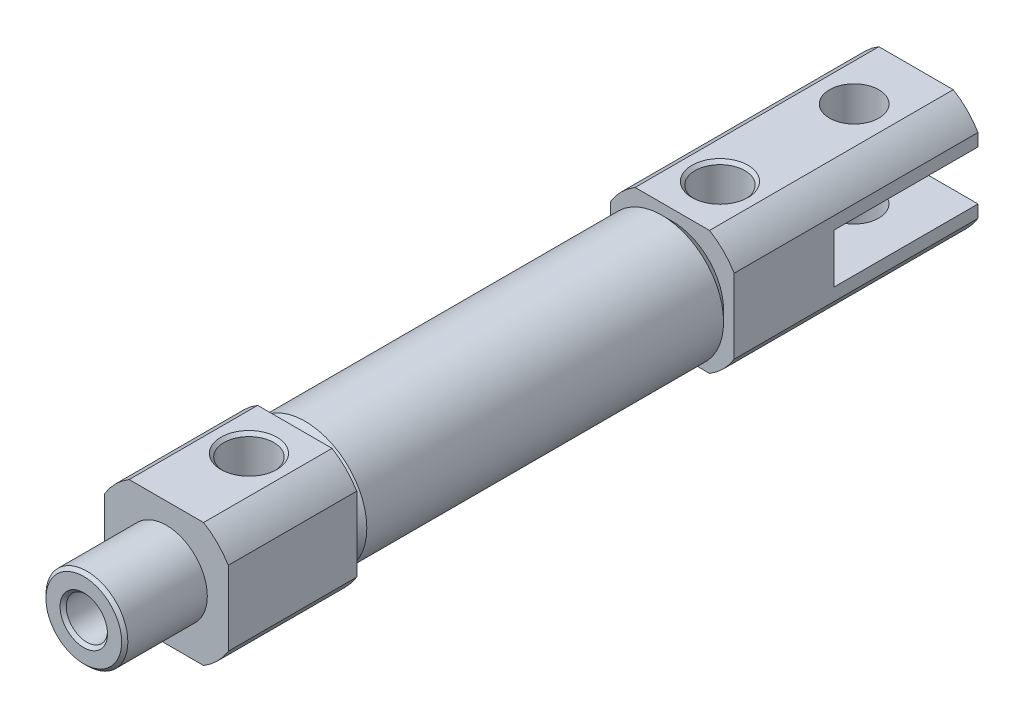
SolidWorks part; units mm, degrees
ref_plane "Front" through (0, 0, 0) normal (0, 0, 1) x (1, 0, 0)
ref_plane "Top" through (0, 0, 0) normal (0, 1, 0) x (1, 0, 0)
ref_plane "Right" through (0, 0, 0) normal (1, 0, 0) x (0, 0, -1)
sketch "Sketch1" plane through (0, 0, 0) normal (0, 0, 1) x (1, 0, 0)
  circle A0 centre (0, 0) radius 5.97
  dimension "D1" = 11.94
extrude "Base-Extrude" add sketch "Sketch1" along normal up to surface (18.285 mm away) and the other way up to surface (18.285 mm away)
chamfer "TubeChamfer" distance 1 angle 45 2 edges at (5.97, 0, 18.285) (5.97, 0, -18.285)
sketch "Sketch2" plane through (0, 0, 18.285) normal (0, 0, 1) x (1, 0, 0)
  line L1 (-3.6056, 6) -> (3.6056, 6)
  line L2 (-6, 3.6056) -> (-6, -3.6056)
  line L3 (-3.6056, -6) -> (3.6056, -6)
  line L4 (6, 3.6056) -> (6, -3.6056)
  arc A0 (6, 3.6056) -> (3.6056, 6) centre (0, 0) ccw
  arc A1 (3.6056, -6) -> (6, -3.6056) centre (0, 0) ccw
  arc A2 (-6, -3.6056) -> (-3.6056, -6) centre (0, 0) ccw
  arc A3 (-3.6056, 6) -> (-6, 3.6056) centre (0, 0) ccw
  point P4 (0, 5.6647)
  point P5 (-5.6647, 0)
  dimension "C" = 14
  dimension "B" = 12
extrude "RodCover" add sketch "Sketch2" along normal blind 12.45
sketch "Sketch3" plane through (0, 0, -18.285) normal (0, 0, -1) x (-1, 0, 0)
  line L1 (-3.6056, 6) -> (3.6056, 6)
  line L2 (-6, 3.6056) -> (-6, -3.6056)
  line L3 (-3.6056, -6) -> (3.6056, -6)
  line L4 (6, 3.6056) -> (6, -3.6056)
  arc A0 (-3.6056, 6) -> (-6, 3.6056) centre (0, 0) ccw
  arc A1 (-6, -3.6056) -> (-3.6056, -6) centre (0, 0) ccw
  arc A2 (3.6056, -6) -> (6, -3.6056) centre (0, 0) ccw
  arc A3 (6, 3.6056) -> (3.6056, 6) centre (0, 0) ccw
  point P1 (-6, 0)
  point P10 (0, 6)
  dimension "C Or 9" = 14
  dimension "B Or 8" = 12
extrude "HeadCover" add sketch "Sketch3" along normal blind 23.62
sketch "Sketch4" plane through (0, 0, 30.735) normal (0, 0, 1) x (1, 0, 0)
  circle A0 centre (0, 0) radius 3.9688
  dimension "NN" = 7.9375
extrude "NoseThreads" add sketch "Sketch4" along normal blind 8
sketch "Sketch5" plane through (0, 0, 0) normal (0, 1, 0) x (1, 0, 0)
  line L0 (3.6056, -30.735) -> (-3.6056, -30.735) construction
  circle A0 centre (0, -22.735) radius 2.415
  dimension "D1" = 4.83
  dimension "GA or GA-T" = 8
extrude "FrontPort" cut sketch "Sketch5" along normal through all
sketch "Sketch7" plane through (0, 0, 0) normal (1, 0, 0) x (0, 0, -1)
  line L0 (22.905, 0) -> (22.905, 22.4987) construction
  line L1 (-17.285, 0) -> (17.285, 0) construction
  line L2 (-20.32, 0) -> (-25.15, 0) construction
  line L3 (-20.32, 0) -> (-25.15, 0) construction
  line L4 (41.905, 3.6056) -> (41.905, -3.6056) construction
  line L5 (22.905, 0) -> (25.32, 0)
  line L6 (25.32, 0) -> (25.32, 5.7)
  line L8 (25.32, 5.7) -> (25.62, 6)
  line L9 (41.905, 6) -> (18.285, 6) construction
  line L10 (25.62, 6) -> (22.905, 6)
  line L11 (22.905, 6) -> (22.905, 0)
  line L12 (25.32, 0) -> (20.49, 0) construction
  point P15 (22.905, 0)
  dimension "D1" = 45
  dimension "GB" = 19
  dimension "D2" = 0.3
revolve "RearTopPort" cut sketch "Sketch7" angle 360 about L0
sketch "Sketch8" plane through (0, 0, 0) normal (1, 0, 0) x (0, 0, -1)
  line L0 (0, 0) -> (70.4928, 0) construction
  line L1 (-17.285, 0) -> (17.285, 0) construction
  line L2 (41.905, 0) -> (41.905, 2.715)
  line L3 (41.905, 3.6056) -> (41.905, 6) construction
  line L4 (41.905, 2.715) -> (41.605, 2.415)
  line L5 (41.605, 2.415) -> (36.905, 2.415)
  line L6 (36.905, 2.415) -> (36.905, 0)
  line L7 (36.905, 0) -> (41.905, 0)
  line L8 (41.905, 3.6056) -> (41.905, -3.6056) construction
  dimension "D1" = 4.83
  dimension "D2" = 5
  dimension "D3" = 45
  dimension "D4" = 0.3
revolve "RearInLinePort" [suppressed] cut sketch "Sketch8" angle 360 about L0
sketch "Sketch9" plane through (0, 0, 30.735) normal (0, 0, 1) x (1, 0, 0)
  line L1 (-5.5, 2.1354) -> (-5.5, -2.1354)
  line L2 (-4.5993, -3.6954) -> (-0.9007, -5.8308)
  line L3 (0.9007, -5.8308) -> (4.5993, -3.6954)
  line L4 (5.5, -2.1354) -> (5.5, 2.1354)
  line L5 (4.5993, 3.6954) -> (0.9007, 5.8308)
  line L6 (-0.9007, 5.8308) -> (-4.5993, 3.6954)
  circle A0 centre (0, 0) radius 5.5 construction
  arc A1 (-4.5993, 3.6954) -> (-5.5, 2.1354) centre (0, 0) ccw
  arc A2 (-5.5, -2.1354) -> (-4.5993, -3.6954) centre (0, 0) ccw
  arc A3 (-0.9007, -5.8308) -> (0.9007, -5.8308) centre (0, 0) ccw
  arc A4 (4.5993, -3.6954) -> (5.5, -2.1354) centre (0, 0) ccw
  arc A5 (5.5, 2.1354) -> (4.5993, 3.6954) centre (0, 0) ccw
  arc A6 (0.9007, 5.8308) -> (-0.9007, 5.8308) centre (0, 0) ccw
  dimension "D2" = 11.8
  dimension "D1" = 11
extrude "6BoreDetail" [suppressed] add sketch "Sketch9" along normal blind 3
sketch "Sketch10" plane through (0, 0, 38.735) normal (0, 0, 1) x (1, 0, 0)
  circle A0 centre (0, 0) radius 2
  dimension "D" = 4
extrude "RodBore" cut sketch "Sketch10" against normal up to surface (47.585 mm away)
sketch "Sketch11" plane through (0, 0, -8.85) normal (0, 0, 1) x (1, 0, 0)
  circle A0 centre (0, 0) radius 5
  dimension "Bore" = 10
extrude "StrokeChamber" cut sketch "Sketch11" against normal up to surface (17.7 mm away)
sketch "Sketch13" plane through (0, 0, 0) normal (1, 0, 0) x (0, 0, -1)
  line L0 (41.905, 3.6056) -> (41.905, -3.6056) construction
  line L1 (41.905, 2.39) -> (27.935, 2.39)
  line L2 (41.905, 2.39) -> (41.905, -2.39)
  line L3 (41.905, -2.39) -> (27.935, -2.39)
  line L4 (27.935, 2.39) -> (27.935, -2.39)
  point P4 (41.905, 0)
  dimension "CX" = 4.78
  dimension "R+U" = 13.97
extrude "D-ClevisSideCut" cut sketch "Sketch13" against normal through all and the other way through all
sketch "Sketch12" plane through (0, 0, 0) normal (0, 1, 0) x (1, 0, 0)
  line L0 (0, -17.285) -> (0, 17.285) construction
  line L1 (-3.6056, 41.905) -> (3.6056, 41.905) construction
  circle A0 centre (0, 35.905) radius 2.39
  dimension "D" = 4.78
  dimension "R" = 6
chamfer "DetailChamfer" distance 0.3 angle 45 3 edges at (3.9688, 0, 38.735) (0, 6, 25.15) (2, 0, 38.735)
ref_plane "SwitchPlaneA" through (0, 0, 7.185) normal (0, 0, -1) x (-1, 0, 0)
ref_plane "SwitchPlaneB" through (0, 0, -7.285) normal (0, 0, 1) x (1, 0, 0)
extrude "Cut-Extrude1" cut sketch "Sketch12" against normal through all both and the other way through all
